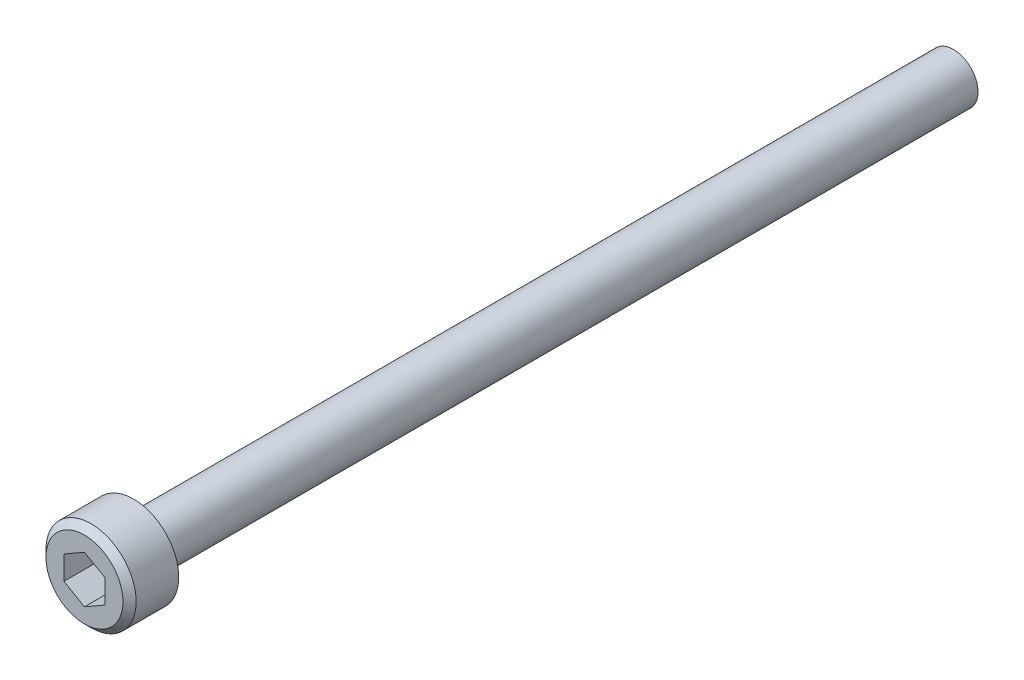
SolidWorks part; units mm, degrees
material "AISI 304"
ref_plane "前视基准面" through (0, 0, 0) normal (0, 0, 1) x (1, 0, 0)
ref_plane "上视基准面" through (0, 0, 0) normal (0, 1, 0) x (1, 0, 0)
ref_plane "右视基准面" through (0, 0, 0) normal (1, 0, 0) x (0, 0, -1)
sketch "草图1" plane through (0, 0, 0) normal (0, 1, 0) x (1, 0, 0)
  line L0 (2.75, 0) -> (0, 0)
  line L1 (0, 0) -> (0, -3)
  line L2 (0, -3) -> (2.75, -3)
  line L3 (2.75, -3) -> (2.75, 0)
  line L4 (0, 0) -> (0, -3) construction
revolve "旋转1" add sketch "草图1" angle 360 about L4
sketch "草图2" plane through (0, 0, 0) normal (0, 0, -1) x (-1, 0, 0)
  circle A0 centre (0, 0) radius 1.5
extrude "凸台-拉伸1" add sketch "草图2" along normal blind 50
sketch "草图3" plane through (0, 0, 3) normal (0, 0, 1) x (1, 0, 0)
  line L0 (1.2485, -0.7243) -> (1.2515, 0.7191)
  line L1 (1.2515, 0.7191) -> (0.003, 1.4434)
  line L2 (0.003, 1.4434) -> (-1.2485, 0.7243)
  line L3 (-1.2485, 0.7243) -> (-1.2515, -0.7191)
  line L4 (-1.2515, -0.7191) -> (-0.003, -1.4434)
  line L5 (-0.003, -1.4434) -> (1.2485, -0.7243)
extrude "切除-拉伸1" cut sketch "草图3" against normal blind 2.5
chamfer "倒角1" distance 0.4 angle 45 1 edges at (2.75, 0, 3)
chamfer "倒角2" distance 0.1 angle 45 1 edges at (-1.5, 0, 0)
